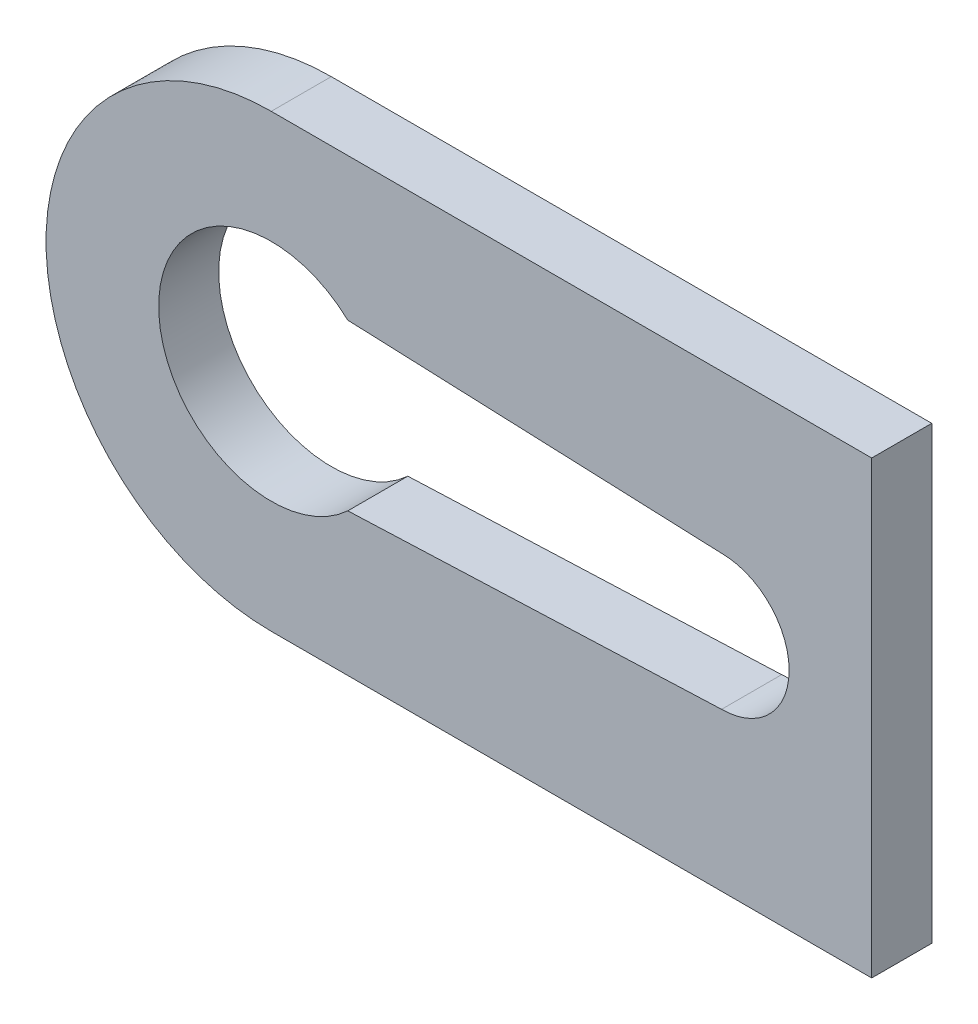
SolidWorks part; units mm, degrees
ref_plane "Front Plane" through (0, 0, 0) normal (0, 0, 1) x (1, 0, 0)
ref_plane "Top Plane" through (0, 0, 0) normal (0, 1, 0) x (1, 0, 0)
ref_plane "Right Plane" through (0, 0, 0) normal (1, 0, 0) x (0, 0, -1)
sketch "Sketch1" plane through (0, 0, 0) normal (0, 0, 1) x (1, 0, 0)
  line L0 (-15, 0) -> (15, 0) construction
  line L1 (-15, 7.5) -> (15, 7.5)
  line L2 (-15, -7.5) -> (15, -7.5)
  line L3 (-15, -9.0753) -> (-15, 9.0753) construction
  line L4 (5, 7.5) -> (5, -7.5)
  line L5 (0, -9.3117) -> (0, 9.3117) construction
  line L6 (-12.4505, 2.75) -> (0, 2.25)
  line L7 (-12.4505, -2.75) -> (0, -2.25)
  line L8 (-12.4505, 2.75) -> (-12.4505, -2.75)
  circle A0 centre (-15, 0) radius 1
  arc A1 (-15, 7.5) -> (-15, -7.5) centre (-15, 0) ccw
  arc A2 (15, -7.5) -> (15, 7.5) centre (15, 0) ccw
  circle A3 centre (15, 0) radius 1
  circle A4 centre (-15, 0) radius 3.75
  circle A5 centre (0, 0) radius 2.25
  point P0 (0, 0)
  point P4 (0, 0)
  point P19 (-15, 0)
  point P22 (0, 0)
  dimension "D1" = 2
  dimension "D3" = 7.5
  dimension "D4" = 2
  dimension "D5" = 7.5
  dimension "D7" = 4.5
  dimension "D2" = 30
  dimension "D6" = 15
  dimension "D8" = 5.5
  dimension "D9" = 5
extrude "Boss-Extrude1" add sketch "Sketch1" along normal blind 2 contours L1 A1 L2 L4 A5 L7 A4 L6
